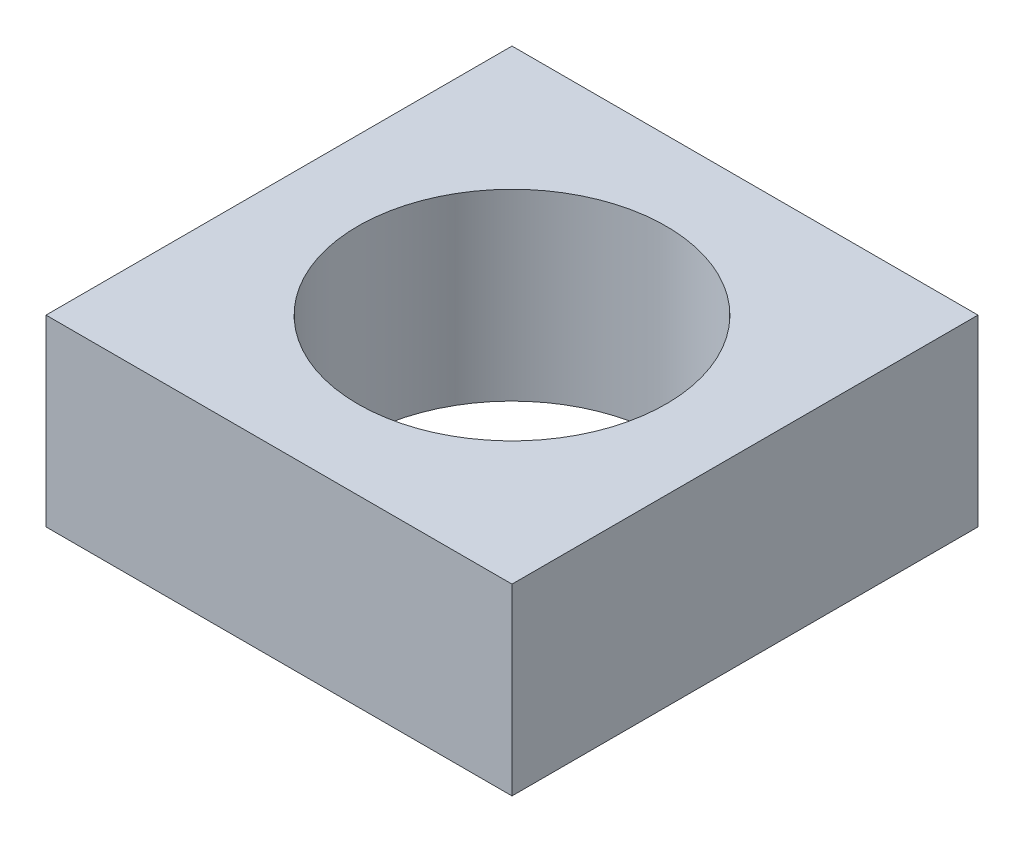
SolidWorks part; units mm, degrees
ref_plane "Front Plane" through (0, 0, 0) normal (0, 0, 1) x (1, 0, 0)
ref_plane "Top Plane" through (0, 0, 0) normal (0, 1, 0) x (1, 0, 0)
ref_plane "Right Plane" through (0, 0, 0) normal (1, 0, 0) x (0, 0, -1)
sketch "Sketch1" plane through (0, 0, 0) normal (0, 1, 0) x (1, 0, 0)
  line L1 (-6.35, -6.35) -> (6.35, -6.35)
  line L2 (-6.35, -6.35) -> (-6.35, 6.35)
  line L3 (-6.35, 6.35) -> (6.35, 6.35)
  line L4 (6.35, -6.35) -> (6.35, 6.35)
  line L5 (-6.35, -6.35) -> (6.35, 6.35) construction
  line L6 (-6.35, 6.35) -> (6.35, -6.35) construction
  circle A0 centre (0, 0) radius 4.2
  point P0 (0, 0)
  dimension "D3" = 8.4
  dimension "D1" = 12.7
  dimension "D2" = 12.7
extrude "Boss-Extrude1" add sketch "Sketch1" along normal blind 5
